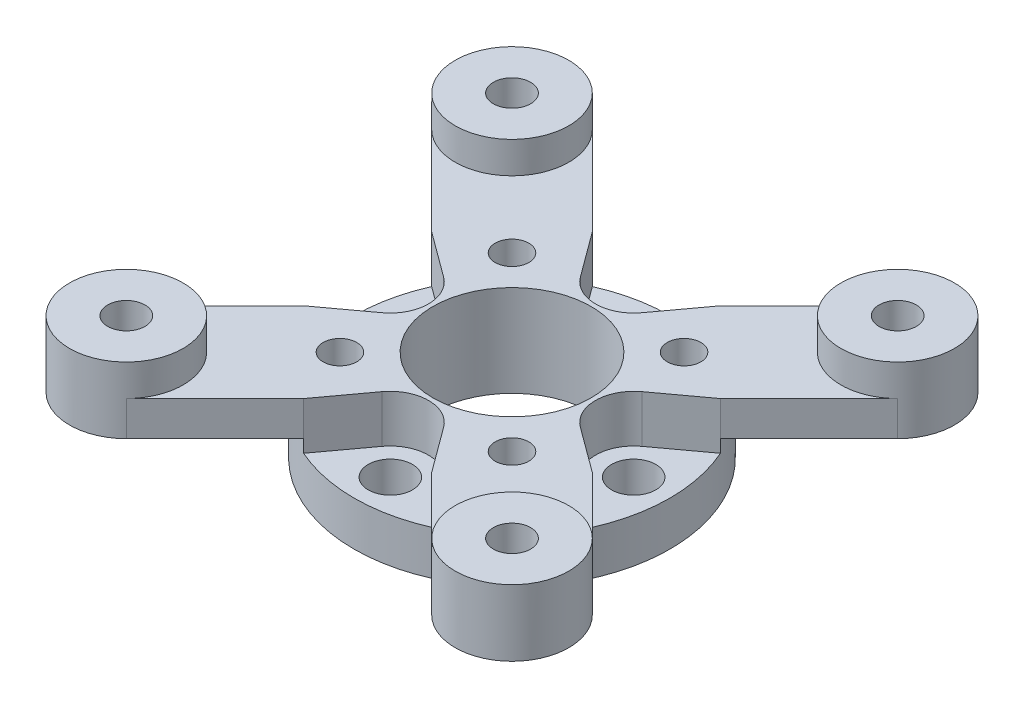
SolidWorks part; units mm, degrees
ref_plane "Front Plane" through (0, 0, 0) normal (0, 0, 1) x (1, 0, 0)
ref_plane "Top Plane" through (0, 0, 0) normal (0, 1, 0) x (1, 0, 0)
ref_plane "Right Plane" through (0, 0, 0) normal (1, 0, 0) x (0, 0, -1)
sketch "Sketch1" plane through (0, 0, 0) normal (0, 0, 1) x (1, 0, 0)
  line L0 (12.6962, 3.556) -> (0, 3.556)
  line L1 (0, 3.556) -> (0, 0)
  line L2 (0, 0) -> (12.6962, 0)
  line L3 (12.6962, 0) -> (12.6962, 3.556)
  line L4 (0, 3.556) -> (0, 0) construction
revolve "Revolve1" add sketch "Sketch1" angle 360 about L4
sketch "Sketch2" plane through (0, 3.556, 0) normal (0, 1, 0) x (-1, 0, 0)
  line L0 (2.4701, 7.9627) -> (5.1486, 11.6054)
  line L1 (11.6054, 5.1486) -> (7.9627, 2.4701)
  line L2 (7.9627, -2.4701) -> (11.6054, -5.1486)
  line L3 (5.1486, -11.6054) -> (2.4701, -7.9627)
  line L4 (-2.4701, -7.9627) -> (-5.1486, -11.6054)
  line L5 (-11.6054, -5.1486) -> (-7.9627, -2.4701)
  line L6 (-7.9627, 2.4701) -> (-11.6054, 5.1486)
  line L7 (-5.1486, 11.6054) -> (-2.4701, 7.9627)
  arc A0 (5.1486, 11.6054) -> (11.6054, 5.1486) centre (0, 0) cw
  arc A1 (7.9627, 2.4701) -> (7.9627, -2.4701) centre (9.779, 0) ccw
  arc A2 (11.6054, -5.1486) -> (5.1486, -11.6054) centre (0, 0) cw
  arc A3 (2.4701, -7.9627) -> (-2.4701, -7.9627) centre (0, -9.779) ccw
  arc A4 (-5.1486, -11.6054) -> (-11.6054, -5.1486) centre (0, 0) cw
  arc A5 (-7.9627, -2.4701) -> (-7.9627, 2.4701) centre (-9.779, 0) ccw
  arc A6 (-11.6054, 5.1486) -> (-5.1486, 11.6054) centre (0, 0) cw
  arc A7 (-2.4701, 7.9627) -> (2.4701, 7.9627) centre (0, 9.779) ccw
extrude "Boss-Extrude1" add sketch "Sketch2" along normal blind 1.016
sketch "Sketch3" plane through (0, 4.572, 0) normal (0, 1, 0) x (-1, 0, 0)
  line L0 (-7.9627, 2.4701) -> (-11.6054, 5.1486)
  line L1 (-11.6054, 5.1486) -> (-18.7284, 12.2716)
  line L2 (-12.2716, 18.7284) -> (-5.1486, 11.6054)
  line L3 (-5.1486, 11.6054) -> (-2.4701, 7.9627)
  line L4 (2.4701, 7.9627) -> (5.1486, 11.6054)
  line L5 (5.1486, 11.6054) -> (12.2716, 18.7284)
  line L6 (18.7284, 12.2716) -> (11.6054, 5.1486)
  line L7 (11.6054, 5.1486) -> (7.9627, 2.4701)
  line L8 (7.9627, -2.4701) -> (11.6054, -5.1486)
  line L9 (11.6054, -5.1486) -> (18.7284, -12.2716)
  line L10 (12.2716, -18.7284) -> (5.1486, -11.6054)
  line L11 (5.1486, -11.6054) -> (2.4701, -7.9627)
  line L12 (-2.4701, -7.9627) -> (-5.1486, -11.6054)
  line L13 (-5.1486, -11.6054) -> (-12.2716, -18.7284)
  line L14 (-18.7284, -12.2716) -> (-11.6054, -5.1486)
  line L15 (-11.6054, -5.1486) -> (-7.9627, -2.4701)
  arc A0 (-18.7284, 12.2716) -> (-12.2716, 18.7284) centre (-15.5, 15.5) cw
  arc A1 (-2.4701, 7.9627) -> (2.4701, 7.9627) centre (0, 9.779) ccw
  arc A2 (12.2716, 18.7284) -> (18.7284, 12.2716) centre (15.5, 15.5) cw
  arc A3 (7.9627, 2.4701) -> (7.9627, -2.4701) centre (9.779, 0) ccw
  arc A4 (18.7284, -12.2716) -> (12.2716, -18.7284) centre (15.5, -15.5) cw
  arc A5 (2.4701, -7.9627) -> (-2.4701, -7.9627) centre (0, -9.779) ccw
  arc A6 (-12.2716, -18.7284) -> (-18.7284, -12.2716) centre (-15.5, -15.5) cw
  arc A7 (-7.9627, -2.4701) -> (-7.9627, 2.4701) centre (-9.779, 0) ccw
extrude "Boss-Extrude2" add sketch "Sketch3" along normal blind 2.794
sketch "Sketch4" plane through (0, 7.366, 0) normal (0, 1, 0) x (-1, 0, 0)
  circle A0 centre (-15.5, -15.5) radius 4.5656
extrude "Boss-Extrude3" add sketch "Sketch4" along normal blind 2.54
sketch "Sketch5" plane through (0, 7.366, 0) normal (0, 1, 0) x (-1, 0, 0)
  circle A0 centre (15.5, -15.5) radius 4.5656
extrude "Boss-Extrude4" add sketch "Sketch5" along normal blind 2.54
sketch "Sketch6" plane through (0, 7.366, 0) normal (0, 1, 0) x (-1, 0, 0)
  circle A0 centre (15.5, 15.5) radius 4.5656
extrude "Boss-Extrude5" add sketch "Sketch6" along normal blind 2.54
sketch "Sketch7" plane through (0, 7.366, 0) normal (0, 1, 0) x (-1, 0, 0)
  circle A0 centre (-15.5, 15.5) radius 4.5656
extrude "Boss-Extrude6" add sketch "Sketch7" along normal blind 2.54
hole_wizard "Hole1" positions "Sketch9" profile "Sketch8" legacy
sketch "Sketch9" plane through (0, 7.366, 0) normal (0, 1, 0) x (1, 0, 0)
  point P0 (0, 0)
sketch "Sketch8" plane through (0, 7.366, 0) normal (1, 0, 0) x (0, 0, 1)
  line L0 (0, 0) -> (0, 7.366)
  line L1 (0, 7.366) -> (6.3627, 7.366)
  line L2 (6.3627, 7.366) -> (6.3627, 0)
  line L3 (6.3627, 0) -> (0, 0)
  line L4 (0, 110) -> (0, -10) construction
  dimension "Diameter" = 12.7254
  dimension "Depth" = 7.366
hole_wizard "M2.5 Clearance Hole1" positions "Sketch11" profile "Sketch10" hole size "M2.5" standard "ANSI Metric"
sketch "Sketch11" plane through (0, 7.366, 0) normal (0, 1, 0) x (1, 0, 0)
  point P0 (6.9148, -6.9148)
  point P1 (-6.9148, 6.9148)
  point P2 (6.9148, 6.9148)
  point P3 (-6.9148, -6.9148)
sketch "Sketch10" plane through (6.9148, 7.366, 6.9148) normal (1, 0, 0) x (0, 0, 1)
  line L0 (0, 0) -> (0, 7.366)
  line L1 (0, 7.366) -> (1.3525, 7.366)
  line L2 (1.3525, 7.366) -> (1.3525, 0)
  line L5 (1.3525, 0) -> (0, 0)
  line L11 (0, -6.35) -> (0, 107.95) construction
  dimension "Thru Hole Dia." = 2.7051
  dimension "Thru Hole Depth" = 7.366
hole_wizard "M3 Clearance Hole1" positions "Sketch13" profile "Sketch12" hole size "M3" standard "ANSI Metric"
sketch "Sketch13" plane through (0, 3.556, 0) normal (0, 1, 0) x (1, 0, 0)
  point P0 (0, -9.779)
  point P1 (-9.779, 0)
  point P2 (0, 9.779)
  point P3 (9.779, 0)
sketch "Sketch12" plane through (0, 3.556, 9.779) normal (1, 0, 0) x (0, 0, 1)
  line L0 (0, 0) -> (0, 3.556)
  line L1 (0, 3.556) -> (1.778, 3.556)
  line L2 (1.778, 3.556) -> (1.778, 0)
  line L5 (1.778, 0) -> (0, 0)
  line L11 (0, -6.35) -> (0, 107.95) construction
  dimension "Thru Hole Dia." = 3.556
  dimension "Thru Hole Depth" = 3.556
hole_wizard "CBORE for M2.5 Hex Head Machine Screw1" positions "Sketch15" profile "Sketch14" counterbore size "M2.5" standard "ANSI Metric"
sketch "Sketch15" plane through (0, 4.572, 0) normal (0, -1, 0) x (-1, 0, 0)
  point P0 (-15.5, 15.5)
  point P1 (15.5, 15.5)
  point P2 (15.5, -15.5)
  point P3 (-15.5, -15.5)
sketch "Sketch14" plane through (15.5, 4.572, -15.5) normal (1, 0, 0) x (0, 0, -1)
  line L0 (0, 0) -> (0, 5.334)
  line L1 (0, 5.334) -> (1.5, 5.334)
  line L3 (1.5, 5.334) -> (1.5, 3.048)
  line L4 (1.5, 3.048) -> (3.175, 3.048)
  line L5 (3.175, 3.048) -> (3.175, 0)
  line L7 (3.175, 0) -> (0, 0)
  line L11 (0, -6.35) -> (0, 107.95) construction
  dimension "Thru Hole Dia." = 3
  dimension "Thru Hole Depth" = 5.334
  dimension "C'Bore Dia." = 6.35
  dimension "C'Bore Depth" = 3.048
